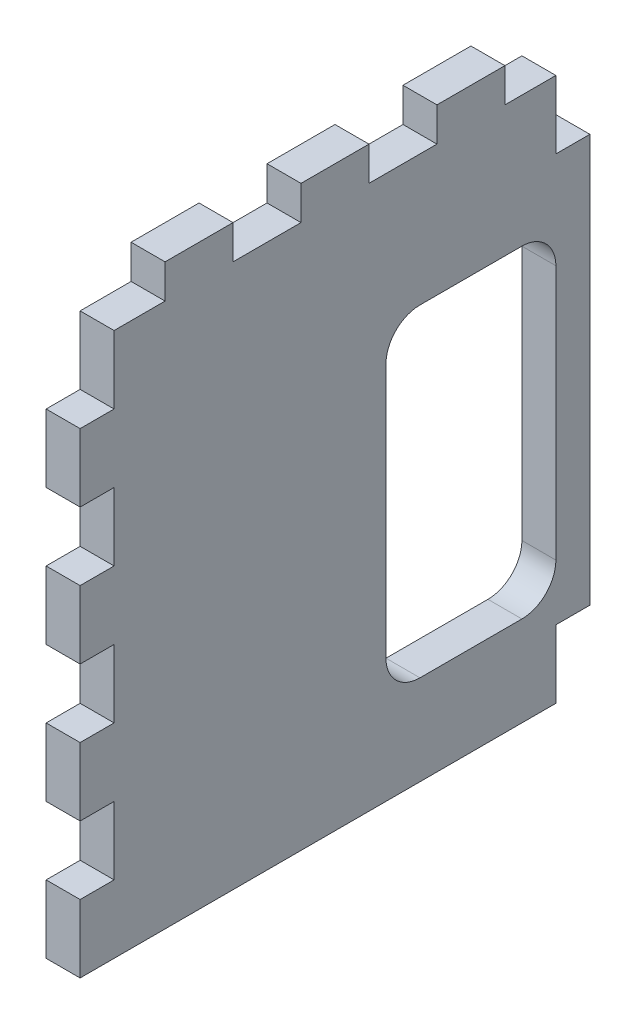
SolidWorks part; units mm, degrees
material "Pine"
ref_plane "Front Plane" through (0, 0, 0) normal (0, 0, 1) x (1, 0, 0)
ref_plane "Top Plane" through (0, 0, 0) normal (0, 1, 0) x (1, 0, 0)
ref_plane "Right Plane" through (0, 0, 0) normal (1, 0, 0) x (0, 0, -1)
sketch "Sketch1" plane through (0, 0, 0) normal (1, 0, 0) x (0, 0, -1)
  line L1 (0, 0) -> (95.25, 0)
  line L2 (0, 0) -> (0, 107.95)
  line L3 (0, 107.95) -> (95.25, 107.95)
  line L4 (95.25, 0) -> (95.25, 107.95)
  dimension "D1" = 95.25
  dimension "D2" = 107.95
extrude "Boss-Extrude1" add sketch "Sketch1" along normal blind 6.35
sketch "Sketch2" plane through (6.35, 0, 0) normal (1, 0, 0) x (0, 0, -1)
  line L0 (73.025, 46.9875) -> (73.025, 63.5) construction
  line L1 (80.899, 13.0785) -> (65.151, 13.0785) construction
  line L2 (80.899, 13.0785) -> (80.899, 80.8965) construction
  line L3 (80.899, 80.8965) -> (65.151, 80.8965) construction
  line L4 (65.151, 13.0785) -> (65.151, 80.8965) construction
  line L5 (80.899, 13.0785) -> (65.151, 80.8965) construction
  line L6 (80.899, 80.8965) -> (65.151, 13.0785) construction
  line L7 (88.9, 16.825) -> (57.15, 16.825)
  line L8 (88.9, 16.825) -> (88.9, 77.15)
  line L9 (88.9, 77.15) -> (57.15, 77.15)
  line L10 (57.15, 16.825) -> (57.15, 77.15)
  line L11 (88.9, 16.825) -> (57.15, 77.15) construction
  line L12 (88.9, 77.15) -> (57.15, 16.825) construction
  line L13 (95.25, 107.95) -> (0, 107.95) construction
  line L15 (95.25, 0) -> (95.25, 107.95) construction
  circle A0 centre (65.151, 80.8965) radius 1.75 construction
  circle A1 centre (80.899, 80.8965) radius 1.75 construction
  circle A2 centre (65.151, 13.0785) radius 1.75 construction
  circle A3 centre (80.899, 13.0785) radius 1.75 construction
  point P0 (73.025, 46.9875)
  point P5 (73.025, 46.9875)
  dimension "D5" = 3.5
  dimension "D1" = 15.748
  dimension "D2" = 67.818
  dimension "D3" = 31.75
  dimension "D4" = 60.325
  dimension "D6" = 13.65
  dimension "D7" = 44.45
  dimension "D8" = 22.225
extrude "Cut-Extrude1" cut sketch "Sketch2" against normal through all
sketch "Sketch3" plane through (6.35, 0, 0) normal (1, 0, 0) x (0, 0, -1)
  line L0 (95.25, 107.95) -> (0, 107.95) construction
  line L1 (0, 107.95) -> (15.875, 107.95)
  line L2 (0, 107.95) -> (0, 101.6)
  line L3 (0, 101.6) -> (15.875, 101.6)
  line L4 (15.875, 107.95) -> (15.875, 101.6)
  line L5 (28.575, 107.95) -> (41.275, 107.95)
  line L6 (28.575, 107.95) -> (28.575, 101.6)
  line L7 (28.575, 101.6) -> (41.275, 101.6)
  line L8 (41.275, 107.95) -> (41.275, 101.6)
  line L10 (53.975, 107.95) -> (66.675, 107.95)
  line L11 (53.975, 107.95) -> (53.975, 101.6)
  line L12 (53.975, 101.6) -> (66.675, 101.6)
  line L13 (66.675, 107.95) -> (66.675, 101.6)
  line L14 (95.25, 107.95) -> (79.375, 107.95)
  line L15 (95.25, 107.95) -> (95.25, 101.6)
  line L16 (95.25, 101.6) -> (79.375, 101.6)
  line L17 (79.375, 107.95) -> (79.375, 101.6)
  dimension "D1" = 12.7
  dimension "D2" = 12.7
  dimension "D3" = 12.7
  dimension "D4" = 12.7
  dimension "D5" = 6.35
extrude "Cut-Extrude2" cut sketch "Sketch3" against normal through all
sketch "Sketch5" plane through (6.35, 0, 0) normal (1, 0, 0) x (0, 0, -1)
  line L1 (95.25, 101.6) -> (88.9, 101.6)
  line L2 (95.25, 101.6) -> (95.25, 88.9)
  line L3 (95.25, 88.9) -> (88.9, 88.9)
  line L4 (88.9, 101.6) -> (88.9, 88.9)
  line L5 (95.25, 0) -> (88.9, 0)
  line L6 (95.25, 0) -> (95.25, 12.7)
  line L7 (95.25, 12.7) -> (88.9, 12.7)
  line L8 (88.9, 0) -> (88.9, 12.7)
  dimension "D1" = 6.35
  dimension "D2" = 12.7
  dimension "D3" = 12.7
extrude "Cut-Extrude3" cut sketch "Sketch5" against normal through all
sketch "Sketch6" plane through (6.35, 0, 0) normal (1, 0, 0) x (0, 0, -1)
  line L1 (0, 101.6) -> (6.35, 101.6)
  line L2 (0, 101.6) -> (0, 88.9)
  line L3 (0, 88.9) -> (6.35, 88.9)
  line L4 (6.35, 101.6) -> (6.35, 88.9)
  dimension "D1" = 6.35
  dimension "D2" = 12.7
extrude "Cut-Extrude4" cut sketch "Sketch6" against normal through all
pattern_linear "LPattern1" count 5 spacing 25.4 along (0, -1, 0) of "Cut-Extrude4"
fillet "Fillet1" radius 6.35 4 edges at (3.175, 16.825, -57.15) (3.175, 16.825, -88.9) (3.175, 77.15, -88.9) (3.175, 77.15, -57.15)
